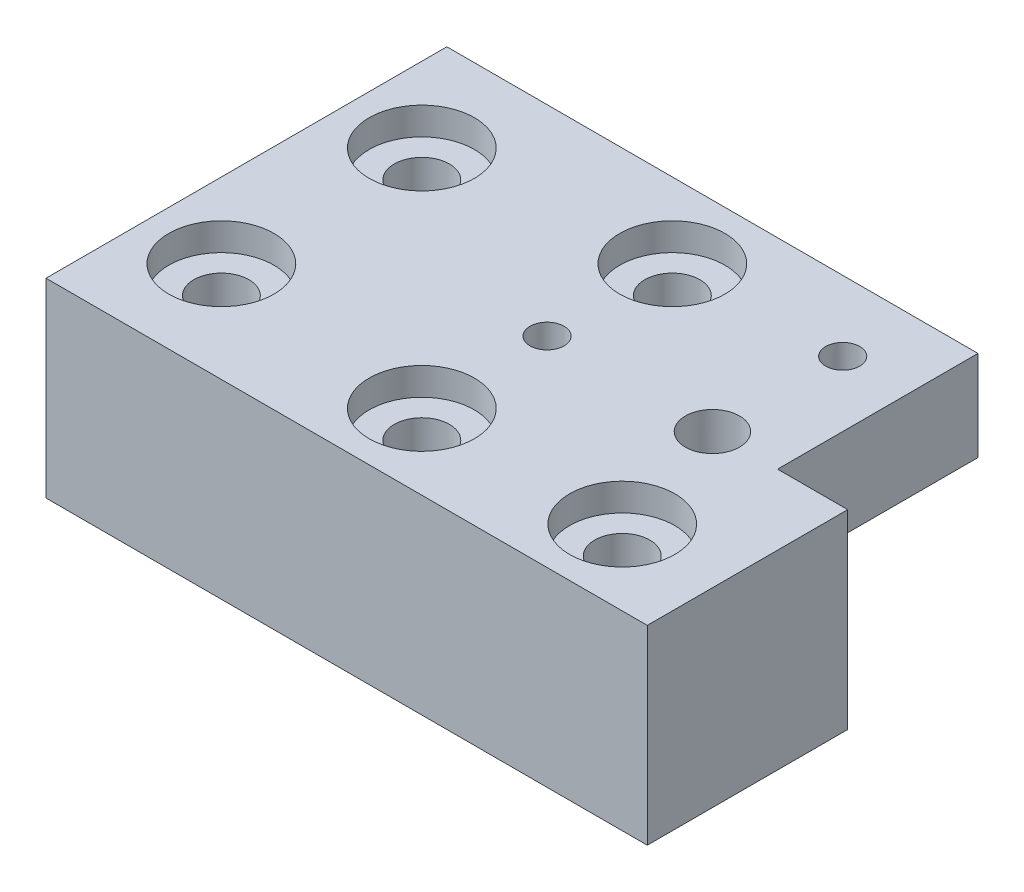
SolidWorks part; units mm, degrees
ref_plane "Front Plane" through (0, 0, 0) normal (0, 0, 1) x (1, 0, 0)
ref_plane "Top Plane" through (0, 0, 0) normal (0, 1, 0) x (1, 0, 0)
ref_plane "Right Plane" through (0, 0, 0) normal (1, 0, 0) x (0, 0, -1)
sketch "Sketch1" plane through (0, 0, 0) normal (0, 1, 0) x (1, 0, 0)
  line L0 (20, 30) -> (60, 30) construction
  line L1 (0, 0) -> (60, 0)
  line L2 (0, 0) -> (0, 20)
  line L4 (60, 0) -> (60, 40)
  line L5 (0, 10) -> (60, 10) construction
  line L6 (50, 0) -> (50, 40) construction
  line L7 (10, 0) -> (10, 20) construction
  line L8 (30, 0) -> (30, 40) construction
  line L9 (20, 40) -> (20, 0) construction
  line L10 (60, 20) -> (0, 20) construction
  line L11 (40, 40) -> (40, 0) construction
  line L12 (20, 40) -> (60, 40)
  line L13 (0, 20) -> (20, 20)
  line L14 (20, 20) -> (20, 40)
  dimension "D2" = 40
  dimension "D3" = 20
  dimension "D5" = 10
  dimension "D6" = 20
  dimension "D7" = 20
  dimension "D8" = 10
  dimension "D9" = 10
extrude "Boss-Extrude1" add sketch "Sketch1" along normal blind 10
sketch "Sketch2" plane through (0, 10, 0) normal (0, 1, 0) x (1, 0, 0)
  line L0 (13.5, 40) -> (13.5, 20) construction
  line L1 (20, 40) -> (7, 40)
  line L4 (7, 40) -> (7, 20)
  line L5 (20, 20) -> (0, 20) construction
  line L6 (0, 20) -> (0, 0)
  line L7 (0, 0) -> (60, 0)
  line L8 (60, 0) -> (60, 40)
  line L9 (60, 40) -> (20, 40)
  line L10 (20, 40) -> (20, 20)
  line L11 (20, 20) -> (0, 20)
  line L12 (0, 20) -> (0, 0)
  line L13 (0, 0) -> (60, 0)
  line L14 (60, 0) -> (60, 40)
  line L15 (60, 40) -> (20, 40)
  line L17 (7, 20) -> (0, 20)
  line L20 (30, 0) -> (30, 40) construction
  point P12 (13.5, 33)
  point P13 (13.5, 20)
  point P14 (30, 20)
  dimension "D2" = 13
  dimension "D3" = 7
  dimension "D4" = 13
  dimension "D1" = 0
extrude "Boss-Extrude2" add sketch "Sketch2" along normal blind 9
hole_wizard "CBORE for M5 SBHCS1" positions "Sketch3" profile "Sketch4" counterbore size "M5" standard "ANSI Metric" end condition through all
sketch "Sketch3" plane through (0, 19, 0) normal (0, 1, 0) x (1, 0, 0)
  line L0 (10, 0) -> (10, 20) construction
  line L1 (30, 0) -> (30, 40) construction
  line L4 (0, 0) -> (60, 0) construction
  line L5 (20, 40) -> (60, 40) construction
  point P0 (10, 7.5)
  point P4 (30, 7.5)
  point P16 (30, 32.5)
  dimension "D1" = 7.5
  dimension "D2" = 7.5
sketch "Sketch4" plane through (10, 19, -7.5) normal (1, 0, 0) x (0, 0, 1)
  line L0 (0, 0) -> (0, 19)
  line L1 (0, 19) -> (2.75, 19)
  line L3 (2.75, 19) -> (2.75, 2.75)
  line L4 (2.75, 2.75) -> (5.25, 2.75)
  line L5 (5.25, 2.75) -> (5.25, 0)
  line L7 (5.25, 0) -> (0, 0)
  line L11 (0, -6.35) -> (0, 107.95) construction
  dimension "Thru Hole Dia." = 5.5
  dimension "Thru Hole Depth" = 19
  dimension "C'Bore Dia." = 10.5
  dimension "C'Bore Depth" = 2.75
hole_wizard "CBORE for M5 SBHCS2" positions "Sketch5" profile "Sketch6" counterbore size "M5" standard "ANSI Metric" end condition through all
sketch "Sketch5" plane through (0, 19, 0) normal (0, 1, 0) x (1, 0, 0)
  line L0 (20, 30) -> (60, 30) construction
  line L1 (0, 10) -> (60, 10) construction
  line L2 (60, 0) -> (60, 40) construction
  point P0 (52.5, 30)
  point P4 (52.5, 10)
  dimension "D1" = 7.5
sketch "Sketch6" plane through (52.5, 19, -30) normal (1, 0, 0) x (0, 0, 1)
  line L0 (0, 0) -> (0, 19)
  line L1 (0, 19) -> (2.75, 19)
  line L3 (2.75, 19) -> (2.75, 2.75)
  line L4 (2.75, 2.75) -> (5.25, 2.75)
  line L5 (5.25, 2.75) -> (5.25, 0)
  line L7 (5.25, 0) -> (0, 0)
  line L11 (0, -6.35) -> (0, 107.95) construction
  dimension "Thru Hole Dia." = 5.5
  dimension "Thru Hole Depth" = 19
  dimension "C'Bore Dia." = 10.5
  dimension "C'Bore Depth" = 2.75
hole_wizard "CBORE for M3 SBHCS1" positions "Sketch9" profile "Sketch10" counterbore size "M3" standard "ANSI Metric" end condition through all
sketch "Sketch9" plane through (0, 0, 0) normal (0, -1, 0) x (-1, 0, 0)
  line L0 (-30, 0) -> (-30, 40) construction
  point P0 (-30, 20)
sketch "Sketch10" plane through (30, 0, -20) normal (1, 0, 0) x (0, 0, -1)
  line L0 (0, 0) -> (0, 19)
  line L1 (0, 19) -> (1.7, 19)
  line L3 (1.7, 19) -> (1.7, 16)
  line L4 (1.7, 16) -> (3.35, 16)
  line L5 (3.35, 16) -> (3.35, 0)
  line L7 (3.35, 0) -> (0, 0)
  line L11 (0, -6.35) -> (0, 107.95) construction
  dimension "Thru Hole Dia." = 3.4
  dimension "Thru Hole Depth" = 19
  dimension "C'Bore Dia." = 6.7
  dimension "C'Bore Depth" = 16
hole_wizard "CBORE for M3 SBHCS2" positions "Sketch11" profile "Sketch12" counterbore size "M3" standard "ANSI Metric" end condition through all
sketch "Sketch11" plane through (0, 10, 0) normal (0, -1, 0) x (-1, 0, 0)
  point P0 (-13.5, 33)
sketch "Sketch12" plane through (13.5, 10, -33) normal (1, 0, 0) x (0, 0, -1)
  line L0 (0, 0) -> (0, 9)
  line L1 (0, 9) -> (1.7, 9)
  line L3 (1.7, 9) -> (1.7, 6)
  line L4 (1.7, 6) -> (3.35, 6)
  line L5 (3.35, 6) -> (3.35, 0)
  line L7 (3.35, 0) -> (0, 0)
  line L11 (0, -6.35) -> (0, 107.95) construction
  dimension "Thru Hole Dia." = 3.4
  dimension "Thru Hole Depth" = 9
  dimension "C'Bore Dia." = 6.7
  dimension "C'Bore Depth" = 6
hole_wizard "Ø5.4 (5.4) Diameter Hole1" positions "Sketch13" profile "Sketch14" hole size "Ø5.4" standard "ANSI Metric" end condition through all
sketch "Sketch13" plane through (0, 0, 0) normal (0, -1, 0) x (-1, 0, 0)
  point P0 (-13.5, 20)
sketch "Sketch14" plane through (13.5, 0, -20) normal (1, 0, 0) x (0, 0, -1)
  line L0 (0, 0) -> (0, 19)
  line L1 (0, 19) -> (2.7, 19)
  line L2 (2.7, 19) -> (2.7, 0)
  line L5 (2.7, 0) -> (0, 0)
  line L11 (0, -6.35) -> (0, 107.95) construction
  dimension "Thru Hole Dia." = 5.4
  dimension "Thru Hole Depth" = 19
fillet "Fillet3" [suppressed] radius 9
fillet "Fillet4" [suppressed] radius 9
fillet "Fillet5" [suppressed] radius 3
mirror "Mirror1" about plane through (60, 10, 0) normal (-1, 0, 0) of bodies 107
delete or keep bodies "Body-Delete/Keep 1" type delete bodies bodies 107
